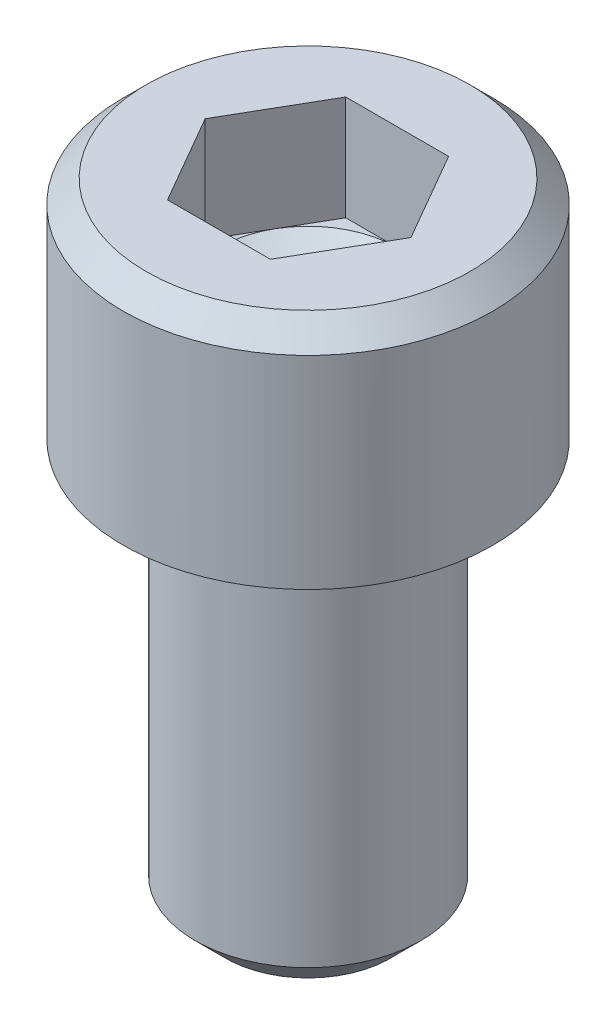
SolidWorks part; units mm, degrees
ref_plane "Front Plane" through (0, 0, 0) normal (0, 0, 1) x (1, 0, 0)
ref_plane "Top Plane" through (0, 0, 0) normal (0, 1, 0) x (1, 0, 0)
ref_plane "Right Plane" through (0, 0, 0) normal (1, 0, 0) x (0, 0, -1)
sketch "Sketch1" plane through (0, 0, 0) normal (0, 0, 1) x (1, 0, 0)
  line L0 (2.8702, 3.5052) -> (0, 3.5052)
  line L1 (0, 3.5052) -> (0, 0)
  line L2 (0, 0) -> (2.8702, 0)
  line L3 (2.8702, 0) -> (2.8702, 3.5052)
  line L4 (0, 3.5052) -> (0, 0) construction
revolve "Revolve1" add sketch "Sketch1" angle 360 about L4
sketch "Sketch2" plane through (0, 0, 0) normal (0, -1, 0) x (1, 0, 0)
  circle A0 centre (0, 0) radius 1.7526
extrude "Boss-Extrude1" add sketch "Sketch2" along normal blind 6.35
sketch "Sketch3" plane through (0, 3.5052, 0) normal (0, 1, 0) x (-1, 0, 0)
  line L0 (-1.5985, 0) -> (-0.7992, -1.3843)
  line L1 (-0.7992, -1.3843) -> (0.7992, -1.3843)
  line L2 (0.7992, -1.3843) -> (1.5985, 0)
  line L3 (1.5985, 0) -> (0.7992, 1.3843)
  line L4 (0.7992, 1.3843) -> (-0.7992, 1.3843)
  line L5 (-0.7992, 1.3843) -> (-1.5985, 0)
extrude "Cut-Extrude1" cut sketch "Sketch3" against normal blind 1.6256
sketch "Sketch4" plane through (0, 0, 0) normal (0, 0, 1) x (1, 0, 0)
  line L0 (1.3843, 1.8796) -> (0, 1.8796)
  line L1 (0, 1.8796) -> (0, 1.0804)
  line L2 (0, 1.0804) -> (1.3843, 1.8796)
  line L3 (0, 1.8796) -> (0, 1.0804) construction
revolve "Cut-Revolve1" cut sketch "Sketch4" angle 360 about L3
chamfer "Chamfer1" distance 0.4724 angle 45 1 edges at (0, -6.35, -1.7526)
chamfer "Chamfer2" distance 0.3556 angle 45 1 edges at (0, 3.5052, -2.8702)
fillet "Fillet1" radius 0.254 1 edges at (0, 0, -1.7526)
